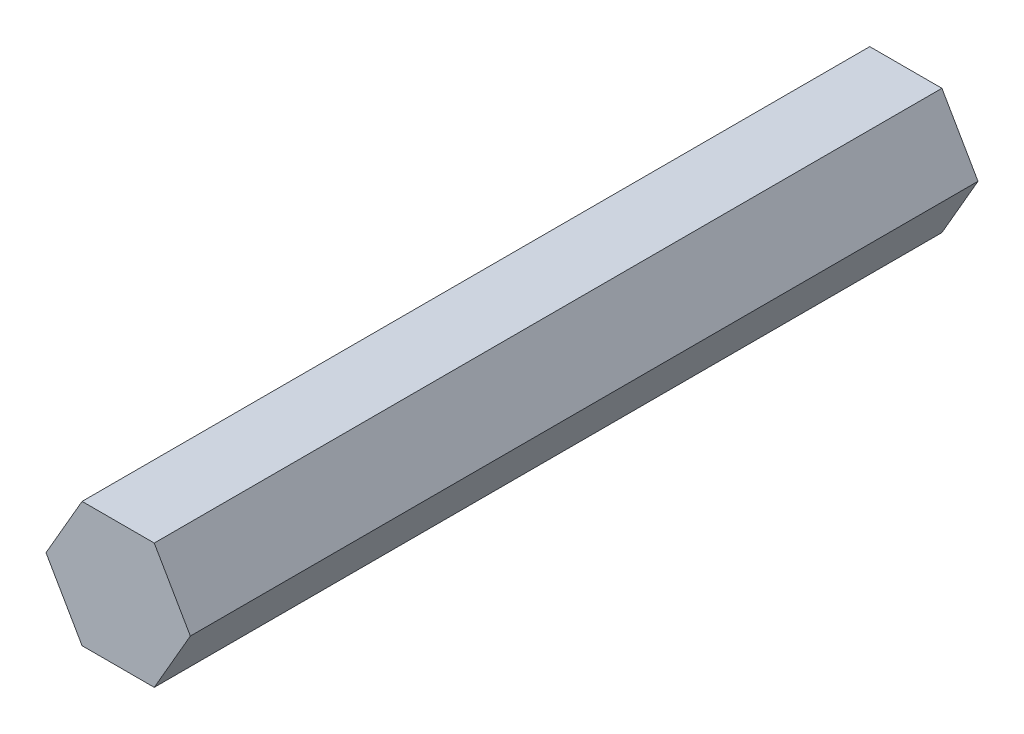
SolidWorks part; units mm, degrees
ref_plane "Front Plane" through (0, 0, 0) normal (0, 0, 1) x (1, 0, 0)
ref_plane "Top Plane" through (0, 0, 0) normal (0, 1, 0) x (1, 0, 0)
ref_plane "Right Plane" through (0, 0, 0) normal (1, 0, 0) x (0, 0, -1)
sketch "Sketch1" plane through (0, 0, 0) normal (0, 0, 1) x (1, 0, 0)
  line L1 (-3.665, 6.348) -> (-7.33, 0)
  line L2 (-7.33, 0) -> (-3.665, -6.348)
  line L3 (-3.665, -6.348) -> (3.665, -6.348)
  line L4 (3.665, -6.348) -> (7.33, 0)
  line L5 (7.33, 0) -> (3.665, 6.348)
  line L6 (3.665, 6.348) -> (-3.665, 6.348)
  circle A0 centre (0, 0) radius 6.348 construction
  point P1 (0, 6.348)
  dimension "D1" = 7.33
extrude "Boss-Extrude1" add sketch "Sketch1" along normal blind 80
